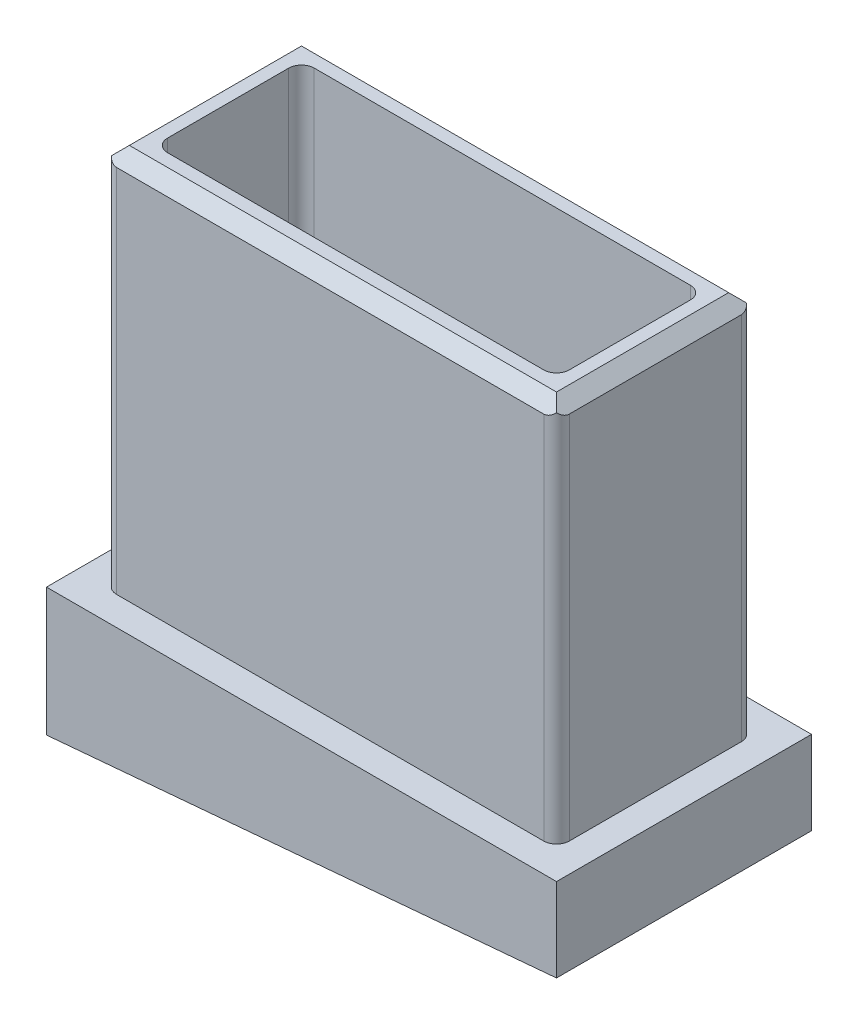
SolidWorks part; units mm, degrees
ref_plane "Front Plane" through (0, 0, 0) normal (0, 0, 1) x (1, 0, 0)
ref_plane "Top Plane" through (0, 0, 0) normal (0, 1, 0) x (1, 0, 0)
ref_plane "Right Plane" through (0, 0, 0) normal (1, 0, 0) x (0, 0, -1)
sketch "Sketch1" plane through (0, 0, 0) normal (0, 0, 1) x (1, 0, 0)
  line L1 (-22.5425, 19.05) -> (22.5425, 19.05)
  line L2 (-22.5425, 19.05) -> (-22.5425, -19.05)
  line L3 (-22.5425, -19.05) -> (22.5425, -19.05)
  line L4 (22.5425, 19.05) -> (22.5425, -19.05)
  line L5 (-22.5425, 19.05) -> (22.5425, -19.05) construction
  line L6 (-22.5425, -19.05) -> (22.5425, 19.05) construction
  point P0 (0, 0)
  dimension "D1" = 38.1
  dimension "D2" = 45.085
extrude "Boss-Extrude1" add sketch "Sketch1" along normal mid plane 19.685
sketch "Sketch2" plane through (0, -19.05, 0) normal (0, -1, 0) x (1, 0, 0)
  line L0 (-22.5425, 9.8425) -> (-22.5425, -9.8425) construction
  line L1 (-25.4, -12.7) -> (25.4, -12.7)
  line L2 (-25.4, -12.7) -> (-25.4, 12.7)
  line L3 (-25.4, 12.7) -> (25.4, 12.7)
  line L4 (25.4, -12.7) -> (25.4, 12.7)
  line L5 (-25.4, -12.7) -> (25.4, 12.7) construction
  line L6 (-25.4, 12.7) -> (25.4, -12.7) construction
  line L8 (-22.5425, -9.8425) -> (22.5425, -9.8425) construction
  point P0 (0, 0)
  dimension "D1" = 2.8575
  dimension "D2" = 2.8575
extrude "Boss-Extrude2" add sketch "Sketch2" along normal blind 12.7635
sketch "Sketch3" plane through (0, 0, 12.7) normal (0, 0, 1) x (1, 0, 0)
  line L0 (25.4, -31.8135) -> (25.4, -27.3691)
  line L1 (25.4, -31.8135) -> (25.4, -19.05) construction
  line L2 (25.4, -27.3691) -> (-25.4, -31.8135)
  line L3 (-25.4, -31.8135) -> (25.4, -31.8135)
  dimension "D1" = 5
extrude "Cut-Extrude1" cut sketch "Sketch3" against normal through all
sketch "Sketch4" plane through (0, 19.05, 0) normal (0, 1, 0) x (1, 0, 0)
  line L0 (-22.5425, -9.8425) -> (-22.5425, 9.8425) construction
  line L1 (-20.0025, 7.3025) -> (20.0025, 7.3025)
  line L2 (-20.0025, 7.3025) -> (-20.0025, -7.3025)
  line L3 (-20.0025, -7.3025) -> (20.0025, -7.3025)
  line L4 (20.0025, 7.3025) -> (20.0025, -7.3025)
  line L5 (-20.0025, 7.3025) -> (20.0025, -7.3025) construction
  line L6 (-20.0025, -7.3025) -> (20.0025, 7.3025) construction
  line L7 (-22.5425, 9.8425) -> (22.5425, 9.8425) construction
  point P0 (0, 0)
  dimension "D1" = 2.54
  dimension "D2" = 2.54
extrude "Cut-Extrude2" cut sketch "Sketch4" against normal blind 38.1
chamfer "Chamfer1" distance 1.27 angle 45 4 edges at (-22.5425, 19.05, 0) (0, 19.05, -9.8425) (22.5425, 19.05, 0) (0, 19.05, 9.8425)
fillet "Fillet1" radius 1.27 8 edges at (22.5425, -0.635, 9.8425) (22.5425, -0.635, -9.8425) (20.0025, 0, 7.3025) (20.0025, 0, -7.3025) (-20.0025, 0, 7.3025) (-20.0025, 0, -7.3025) (-22.5425, -0.635, -9.8425) (-22.5425, -0.635, 9.8425)
equation "\"D2@Sketch2\"=\"D1@Sketch2\""
